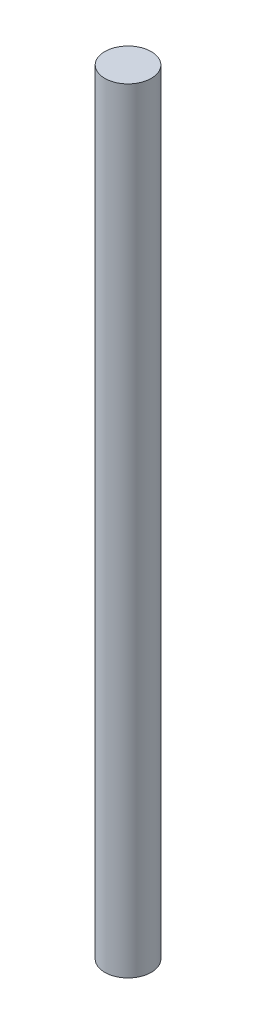
SolidWorks part; units mm, degrees
ref_plane "Front Plane" through (0, 0, 0) normal (0, 0, 1) x (1, 0, 0)
ref_plane "Top Plane" through (0, 0, 0) normal (0, 1, 0) x (1, 0, 0)
ref_plane "Right Plane" through (0, 0, 0) normal (1, 0, 0) x (0, 0, -1)
sketch "Sketch1" plane through (0, 0, 0) normal (0, 0, 1) x (1, 0, 0)
  line L0 (0, 0) -> (0, 150)
  line L1 (0, 0) -> (4.5, 0)
  line L2 (0, 0) -> (0, 150) construction
  line L3 (0, 150) -> (4.5, 150)
  line L4 (4.5, 0) -> (4.5, 150)
  dimension "D1" = 9
  dimension "D2" = 150
revolve "Revolve1" add sketch "Sketch1" angle 360 about L2
